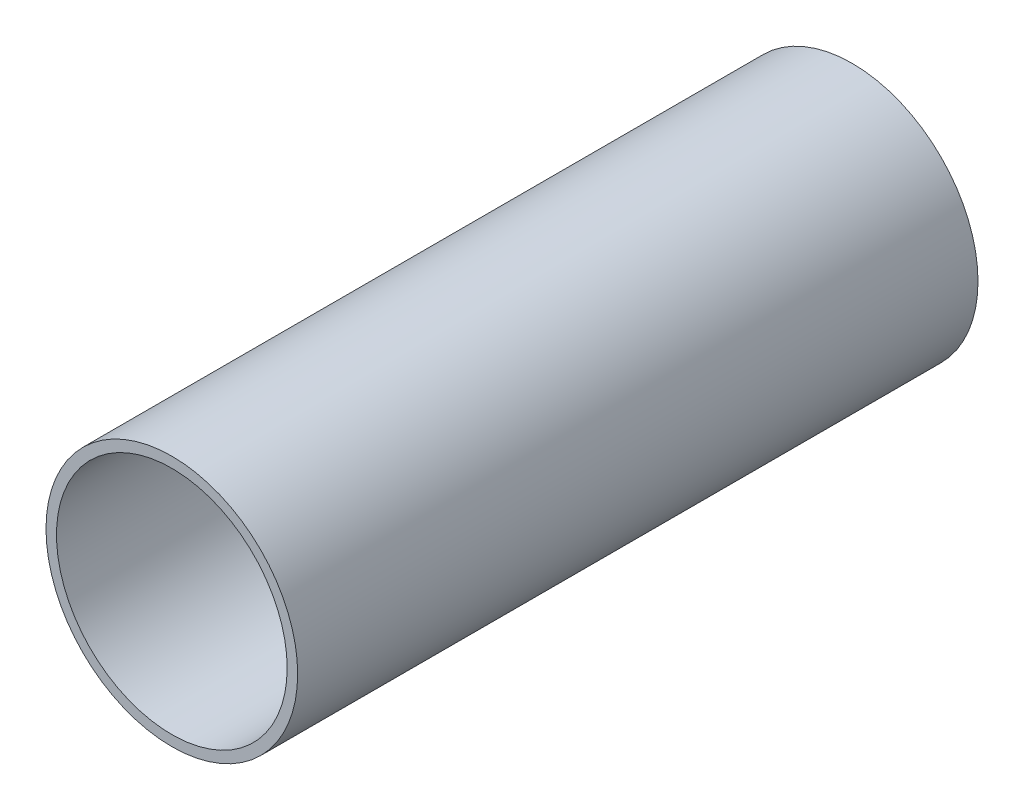
SolidWorks part; units mm, degrees
ref_plane "Front Plane" through (0, 0, 0) normal (0, 0, 1) x (1, 0, 0)
ref_plane "Top Plane" through (0, 0, 0) normal (0, 1, 0) x (1, 0, 0)
ref_plane "Right Plane" through (0, 0, 0) normal (1, 0, 0) x (0, 0, -1)
sketch "Sketch1" plane through (0, 0, 0) normal (0, 0, 1) x (1, 0, 0)
  circle A0 centre (0, 0) radius 76.2
  circle A1 centre (0, 0) radius 69.85
  dimension "D1" = 152.4
  dimension "D2" = 139.7
extrude "Boss-Extrude1" add sketch "Sketch1" along normal blind 412
